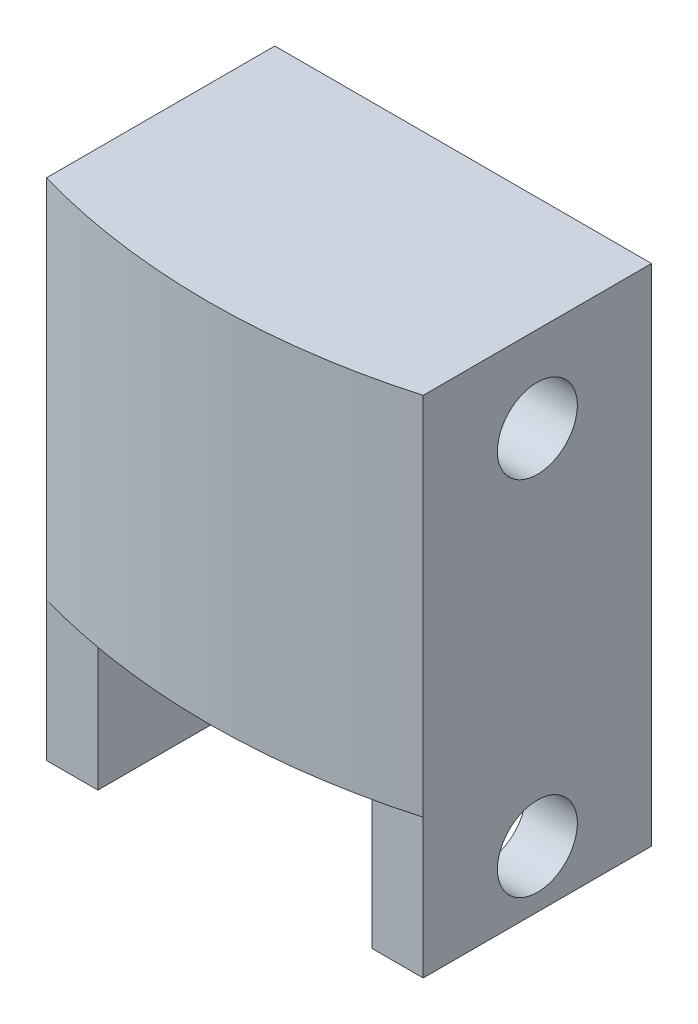
SolidWorks part; units mm, degrees
ref_plane "Front Plane" through (0, 0, 0) normal (0, 0, 1) x (1, 0, 0)
ref_plane "Top Plane" through (0, 0, 0) normal (0, 1, 0) x (1, 0, 0)
ref_plane "Right Plane" through (0, 0, 0) normal (1, 0, 0) x (0, 0, -1)
sketch "Sketch1" plane through (0, 0, 0) normal (0, 1, 0) x (1, 0, 0)
  line L0 (-16.5, 10) -> (16.5, 10)
  line L1 (16.5, 10) -> (16.5, -10)
  line L2 (-16.5, 10) -> (-16.5, -10)
  arc A0 (-16.5, -10) -> (16.5, -10) centre (0, 47.6867) ccw
  point P5 (0, 10)
  point P7 (-16.5, 0)
  dimension "D3" = 60
  dimension "D1" = 33
  dimension "D2" = 20
extrude "Boss-Extrude1" add sketch "Sketch1" along normal blind 32 contours A0 L1 L0 L2
sketch "Sketch3" plane through (-16.5, 0, 0) normal (-1, 0, 0) x (0, 0, 1)
  line L0 (-10, 0) -> (-10, -12.2)
  line L1 (-10, -12.2) -> (10, -12.2)
  line L2 (10, -12.2) -> (10, 0)
  line L3 (10, 0) -> (-10, 0)
  dimension "D1" = 12.2
extrude "Boss-Extrude2" add sketch "Sketch3" against normal blind 4.5
mirror "Mirror1" about plane through (0, 0, 0) normal (1, 0, 0) of "Boss-Extrude2"
sketch "Sketch4" plane through (-16.5, 0, 0) normal (-1, 0, 0) x (0, 0, 1)
  line L0 (-10, -12.2) -> (10, -12.2) construction
  circle A0 centre (0, -7.2) radius 3.5
  dimension "D1" = 7
  dimension "D2" = 5
extrude "Cut-Extrude1" cut sketch "Sketch4" against normal through all
sketch "Sketch5" plane through (16.5, 0, 0) normal (-1, 0, 0) x (0, 0, 1)
  line L0 (-10, 32) -> (10, 32) construction
  circle A0 centre (0, 24.5) radius 3.5
  dimension "D1" = 7
  dimension "D2" = 7.5
extrude "Cut-Extrude2" cut sketch "Sketch5" along normal blind 9
fillet "Fillet1" radius 2.5 2 edges at (12, -6.1, -10)
